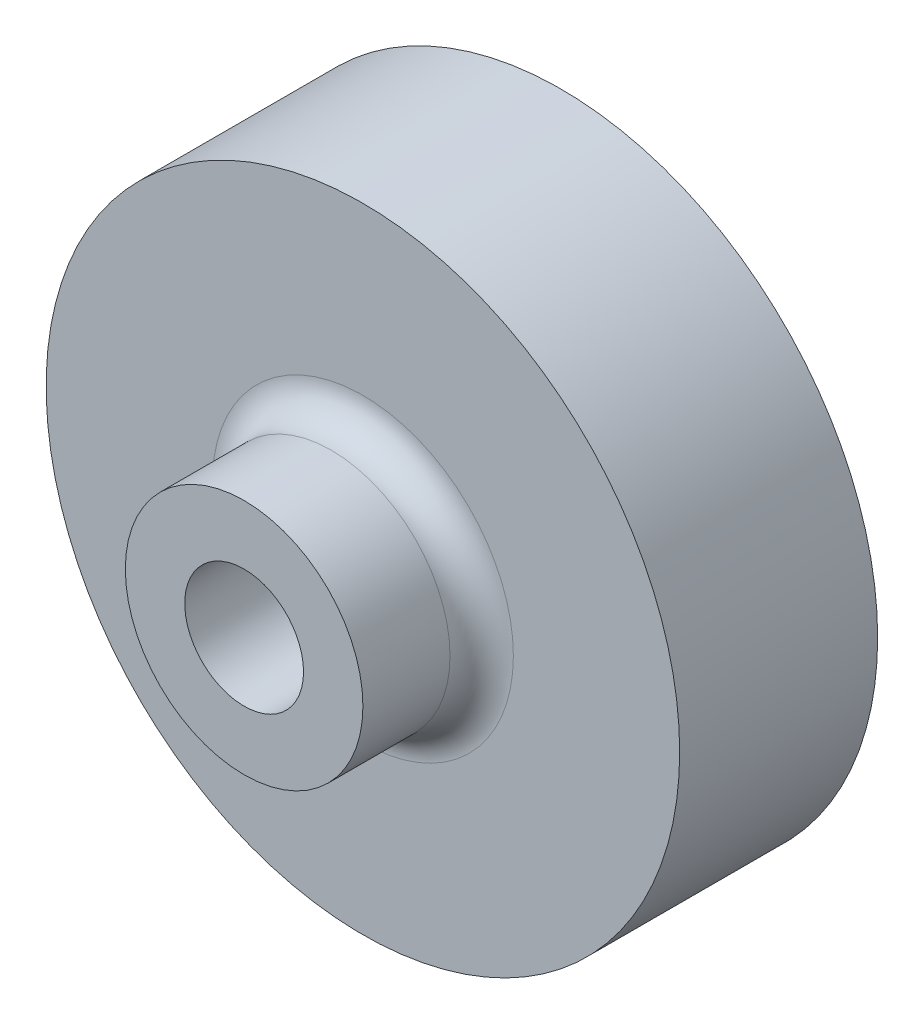
SolidWorks part; units mm, degrees
ref_plane "Front Plane" through (0, 0, 0) normal (0, 0, 1) x (1, 0, 0)
ref_plane "Top Plane" through (0, 0, 0) normal (0, 1, 0) x (1, 0, 0)
ref_plane "Right Plane" through (0, 0, 0) normal (1, 0, 0) x (0, 0, -1)
sketch "Sketch2" plane through (0, 0, 0) normal (0, 0, 1) x (1, 0, 0)
  circle A0 centre (0, 0) radius 25.4
extrude "Boss-Extrude1" add sketch "Sketch2" along normal blind 15.875
sketch "Sketch3" plane through (0, 0, 15.875) normal (0, 0, 1) x (1, 0, 0)
  circle A0 centre (0, 0) radius 9.525
  circle A1 centre (0, 0) radius 4.7625
extrude "Boss-Extrude2" add sketch "Sketch3" along normal blind 9.525
sketch "Sketch4" plane through (0, 0, 15.875) normal (0, 0, 1) x (1, 0, 0)
  circle A0 centre (0, 0) radius 4.7625
extrude "Cut-Extrude2" cut sketch "Sketch4" against normal blind 24.511
sketch "Sketch5" plane through (0, 0, 0) normal (0, 0, -1) x (-1, 0, 0)
  line L2 (0, 4.7625) -> (1.27, 4.7625)
  line L3 (1.27, 4.7625) -> (1.27, 0)
  line L5 (0, -4.7625) -> (1.27, -4.7625)
  line L6 (1.27, -4.7625) -> (1.27, 0)
  line L7 (0, 4.7625) -> (-1.27, 4.7625)
  line L8 (-1.27, 4.7625) -> (-1.27, 0)
  line L9 (-1.27, 0) -> (-1.27, -4.7625)
  line L10 (-1.27, -4.7625) -> (0, -4.7625)
  circle A0 centre (0, 0) radius 4.7625 construction
  point P3 (0, 0)
extrude "Boss-Extrude3" add sketch "Sketch5" against normal blind 3.175
fillet "Fillet1" radius 2.54 1 edges at (9.525, 0, 15.875)
